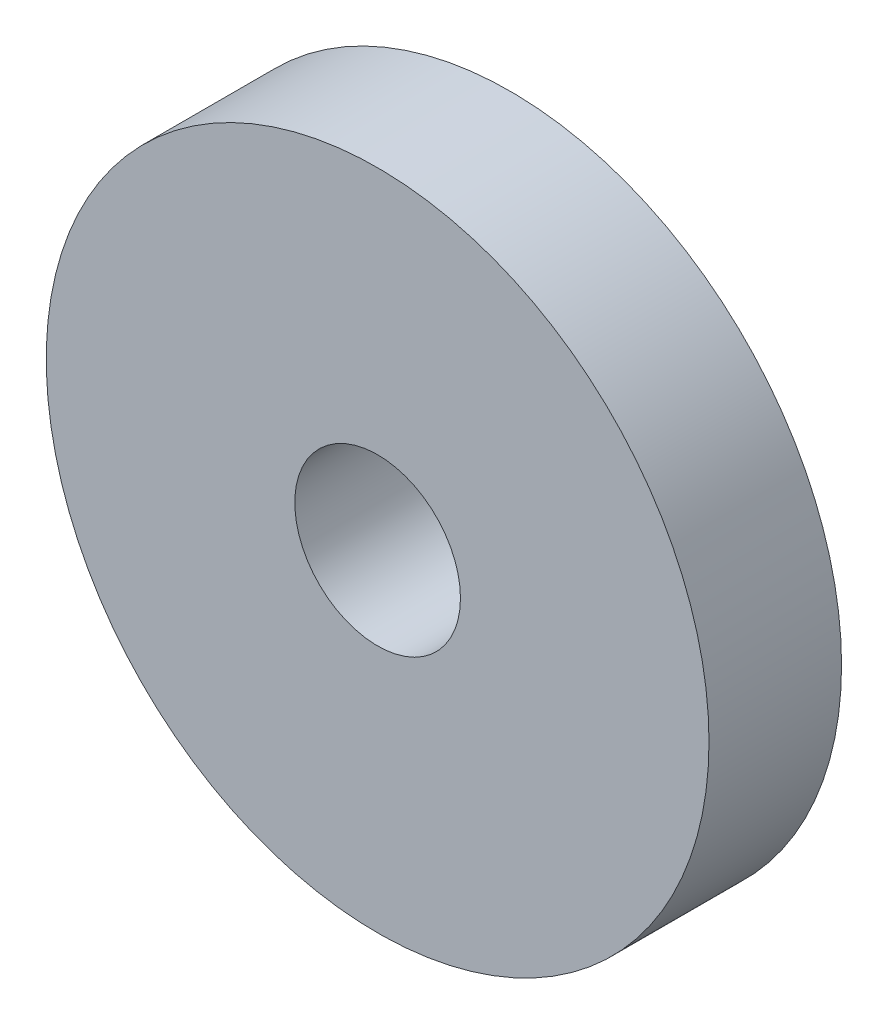
SolidWorks part; units mm, degrees
material "Acrylic (Medium-high impact)"
ref_plane "Front Plane" through (0, 0, 0) normal (0, 0, 1) x (1, 0, 0)
ref_plane "Top Plane" through (0, 0, 0) normal (0, 1, 0) x (1, 0, 0)
ref_plane "Right Plane" through (0, 0, 0) normal (1, 0, 0) x (0, 0, -1)
sketch "Model" plane through (0, 0, 0) normal (0, 0, 1) x (1, 0, 0)
  circle A315 centre (0, 0) radius 1.25
  circle A316 centre (0, 0) radius 5
  dimension "D1" = 2.5
  dimension "D2" = 10
extrude "Boss-Extrude1" add sketch "Model" along normal blind 2
